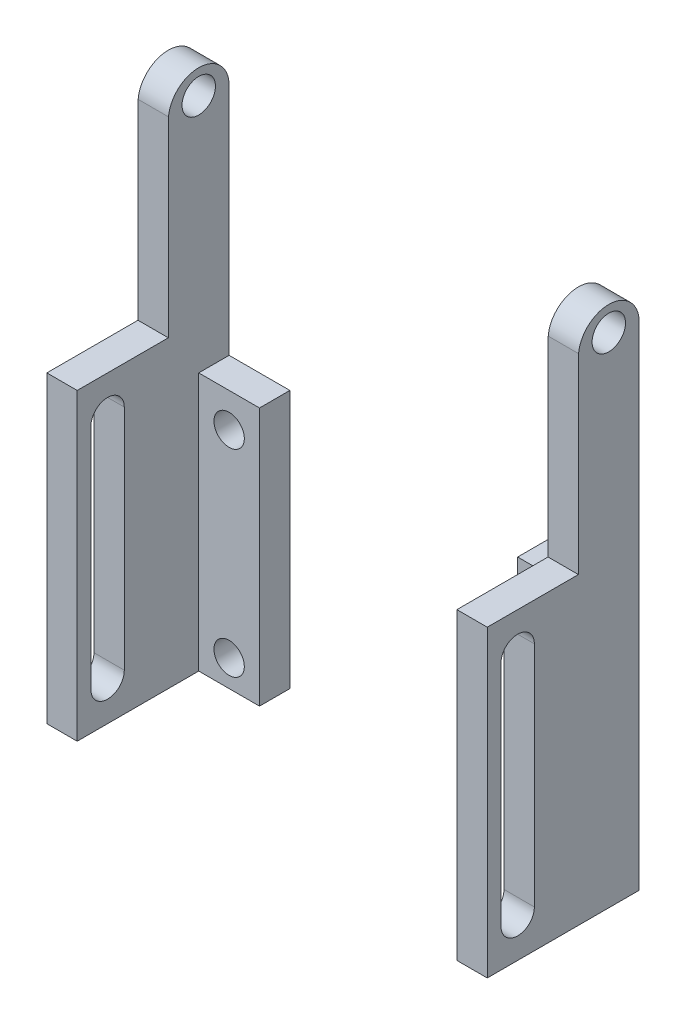
SolidWorks part; units mm, degrees
ref_plane "前视基准面" through (0, 0, 0) normal (0, 0, 1) x (1, 0, 0)
ref_plane "上视基准面" through (0, 0, 0) normal (0, 1, 0) x (1, 0, 0)
ref_plane "右视基准面" through (0, 0, 0) normal (1, 0, 0) x (0, 0, -1)
sketch "草图1" plane through (0, 0, 0) normal (0, 0, 1) x (1, 0, 0)
  line L16 (-39.25, -3) -> (-41.25, -3)
  line L17 (-41.25, -3) -> (-41.25, -7)
  line L18 (-41.25, -7) -> (-39.25, -7)
  line L19 (-39.25, -7) -> (-39.25, -3)
  line L20 (-34.75, -3) -> (-36.75, -3)
  line L21 (-36.75, -3) -> (-36.75, -7)
  line L22 (-36.75, -7) -> (-34.75, -7)
  line L23 (-34.75, -7) -> (-34.75, -3)
  line L24 (-12.25, -3) -> (-14.25, -3)
  line L25 (-14.25, -3) -> (-14.25, -7)
  line L26 (-14.25, -7) -> (-12.25, -7)
  line L27 (-12.25, -7) -> (-12.25, -3)
  line L28 (-7.75, -3) -> (-9.75, -3)
  line L29 (-9.75, -3) -> (-9.75, -7)
  line L30 (-9.75, -7) -> (-7.75, -7)
  line L31 (-7.75, -7) -> (-7.75, -3)
  line L32 (-9.75, -5) -> (-12.25, -5) construction
  line L33 (-36.75, -5) -> (-39.25, -5) construction
  line L34 (-9.75, -3) -> (-39.25, -3) construction
  line L35 (-24.5, -3) -> (-24.5, -18.3575) construction
  line L36 (-38.9967, -3) -> (-36.9967, -3)
  line L37 (-10.0033, -3) -> (-12.0033, -3)
  line L38 (-10.0033, -3) -> (-10.0033, -38)
  line L39 (-10.0033, -38) -> (-12.0033, -38)
  line L40 (-12.0033, -3) -> (-12.0033, -38)
  line L41 (-36.9967, -3) -> (-36.9967, -38)
  line L42 (-38.9967, -3) -> (-38.9967, -38)
  line L43 (-38.9967, -38) -> (-36.9967, -38)
  dimension "D1" = 2
  dimension "D2" = 0.2533
  dimension "D3" = 35
extrude "凸台-拉伸1" add sketch "草图1" against normal blind 4 contours L38 L39 L40 L37 | L41 L43 L42 L36
sketch "草图2" plane through (0, 0, -4) normal (0, 0, -1) x (-1, 0, 0)
  line L1 (36.9967, -38) -> (32.9967, -38)
  line L2 (36.9967, -38) -> (36.9967, -21)
  line L3 (36.9967, -21) -> (32.9967, -21)
  line L4 (38.9967, -3) -> (36.9967, -3)
  line L5 (36.9967, -3) -> (36.9967, -38)
  line L6 (36.9967, -38) -> (38.9967, -38)
  line L7 (38.9967, -38) -> (38.9967, -3)
  line L8 (38.9967, -3) -> (36.9967, -3)
  line L9 (36.9967, -3) -> (36.9967, -38)
  line L10 (36.9967, -38) -> (38.9967, -38)
  line L11 (38.9967, -38) -> (38.9967, -3)
  line L12 (12.0033, -3) -> (10.0033, -3)
  line L13 (10.0033, -3) -> (10.0033, -38)
  line L14 (10.0033, -38) -> (12.0033, -38)
  line L15 (12.0033, -38) -> (12.0033, -3)
  line L16 (12.0033, -3) -> (10.0033, -3)
  line L17 (10.0033, -3) -> (10.0033, -38)
  line L18 (10.0033, -38) -> (12.0033, -38)
  line L19 (12.0033, -38) -> (12.0033, -3)
  line L20 (32.9967, -38) -> (32.9967, -21)
  line L21 (12.0033, -38) -> (16.0033, -38)
  line L22 (12.0033, -38) -> (12.0033, -21)
  line L23 (12.0033, -21) -> (16.0033, -21)
  line L24 (16.0033, -38) -> (16.0033, -21)
  line M14 (36.9967, -3) -> (36.9967, -38)
  dimension "D3" = 4
  dimension "D4" = 17
  dimension "D5" = 4
  dimension "D6" = 17
  dimension "D1" = 0
  dimension "D2" = 0
extrude "凸台-拉伸2" add sketch "草图2" against normal blind 2 contours L20 L1 L3 M14 | L21 L24 L23 L19
sketch "草图3" plane through (0, 0, -4) normal (0, 0, -1) x (-1, 0, 0)
  line L0 (32.9967, -38) -> (16.0033, -38) construction
  line L1 (24.5, -38) -> (24.5, -20.7583) construction
  line L6 (12.0033, -3) -> (10.0033, -3)
  line L7 (10.0033, -3) -> (10.0033, -38)
  line L8 (10.0033, -38) -> (16.0033, -38)
  line L9 (16.0033, -38) -> (16.0033, -21)
  line L10 (16.0033, -21) -> (12.0033, -21)
  line L11 (12.0033, -21) -> (12.0033, -3)
  line L12 (12.0033, -3) -> (10.0033, -3)
  line L13 (10.0033, -3) -> (10.0033, -38)
  line L14 (10.0033, -38) -> (16.0033, -38)
  line L15 (16.0033, -38) -> (16.0033, -21)
  line L16 (16.0033, -21) -> (12.0033, -21)
  line L17 (12.0033, -21) -> (12.0033, -3)
  line L18 (38.9967, -3) -> (36.9967, -3)
  line L19 (36.9967, -3) -> (36.9967, -21)
  line L20 (36.9967, -21) -> (32.9967, -21)
  line L21 (32.9967, -21) -> (32.9967, -38)
  line L22 (32.9967, -38) -> (38.9967, -38)
  line L23 (38.9967, -38) -> (38.9967, -3)
  line L24 (38.9967, -3) -> (36.9967, -3)
  line L25 (36.9967, -3) -> (36.9967, -21)
  line L26 (36.9967, -21) -> (32.9967, -21)
  line L27 (32.9967, -21) -> (32.9967, -38)
  line L28 (32.9967, -38) -> (38.9967, -38)
  line L29 (38.9967, -38) -> (38.9967, -3)
  circle A0 centre (34.9967, -36.2462) radius 1
  circle A1 centre (34.9967, -23.2462) radius 1
  circle A2 centre (14.0033, -23.2462) radius 1
  circle A3 centre (14.0033, -36.2462) radius 1
  dimension "D4" = 2
  dimension "D5" = 2
  dimension "D6" = 2
  dimension "D7" = 2
  dimension "D8" = 13
  dimension "D3" = 17
  dimension "D1" = 0
  dimension "D2" = 0
extrude "切除-拉伸1" cut sketch "草图3" against normal blind 2 contours A0 | A1 | A3 | A2
sketch "草图5" plane through (0, 0, 0) normal (0, 0, 1) x (1, 0, 0)
  line L1 (-10.0033, -38) -> (-12.0033, -38)
  line L2 (-10.0033, -38) -> (-10.0033, -18)
  line L3 (-10.0033, -18) -> (-12.0033, -18)
  line L4 (-10.0033, -3) -> (-12.0033, -3)
  line L5 (-12.0033, -3) -> (-12.0033, -38)
  line L6 (-12.0033, -38) -> (-10.0033, -38)
  line L7 (-10.0033, -38) -> (-10.0033, -3)
  line L8 (-10.0033, -3) -> (-12.0033, -3)
  line L9 (-12.0033, -3) -> (-12.0033, -38)
  line L10 (-12.0033, -38) -> (-10.0033, -38)
  line L11 (-10.0033, -38) -> (-10.0033, -3)
  line L12 (-36.9967, -3) -> (-38.9967, -3)
  line L13 (-38.9967, -3) -> (-38.9967, -38)
  line L14 (-38.9967, -38) -> (-36.9967, -38)
  line L15 (-36.9967, -38) -> (-36.9967, -3)
  line L16 (-36.9967, -3) -> (-38.9967, -3)
  line L17 (-38.9967, -3) -> (-38.9967, -38)
  line L18 (-38.9967, -38) -> (-36.9967, -38)
  line L19 (-36.9967, -38) -> (-36.9967, -3)
  line L20 (-12.0033, -38) -> (-12.0033, -18)
  line L21 (-36.9967, -38) -> (-38.9967, -38)
  line L22 (-36.9967, -38) -> (-36.9967, -18)
  line L23 (-36.9967, -18) -> (-38.9967, -18)
  line L24 (-38.9967, -38) -> (-38.9967, -18)
  line M12 (-12.0033, -3) -> (-12.0033, -38)
  line M13 (-12.0033, -38) -> (-10.0033, -38)
  line M14 (-10.0033, -38) -> (-10.0033, -3)
  dimension "D3" = 20
  dimension "D4" = 20
  dimension "D1" = 0
  dimension "D2" = 0
extrude "凸台-拉伸3" add sketch "草图5" along normal blind 6 contours L3 M14 M12 M13 | L19 L23 L17 L18
sketch "草图6" plane through (-10.0033, 0, 0) normal (1, 0, 0) x (0, 0, -1)
  line L0 (-4, -18) -> (-4, -38) construction
  line L1 (-4, -20.5) -> (-4, -35.5) construction
  line L2 (-2.9, -20.5) -> (-2.9, -35.5)
  line L3 (-5.1, -20.5) -> (-5.1, -35.5)
  line L4 (-6, -18) -> (-6, -38) construction
  line L6 (0, -3) -> (0, -18)
  line L7 (0, -18) -> (-6, -18)
  line L8 (-6, -18) -> (-6, -38)
  line L9 (-6, -38) -> (4, -38)
  line L10 (4, -38) -> (4, -3)
  line L11 (4, -3) -> (0, -3)
  line L12 (0, -3) -> (0, -18)
  line L13 (0, -18) -> (-6, -18)
  line L14 (-6, -18) -> (-6, -38)
  line L15 (-6, -38) -> (4, -38)
  line L16 (4, -38) -> (4, -3)
  line L17 (4, -3) -> (0, -3)
  arc A0 (-2.9, -20.5) -> (-5.1, -20.5) centre (-4, -20.5) ccw
  arc A1 (-5.1, -35.5) -> (-2.9, -35.5) centre (-4, -35.5) ccw
  point P10 (-4, -28)
  dimension "D2" = 2.2
  dimension "D3" = 15
  dimension "D4" = 2
  dimension "D1" = 0
extrude "切除-拉伸2" cut sketch "草图6" against normal through all contours L3 A1 L2 A0
sketch "草图7" plane through (-10.0033, 0, 0) normal (1, 0, 0) x (0, 0, -1)
  line L0 (2, -6.3) -> (2, -4.1) construction
  line L6 (0, -3) -> (0, -18)
  line L7 (0, -18) -> (-6, -18)
  line L8 (-6, -18) -> (-6, -38)
  line L9 (-6, -38) -> (4, -38)
  line L10 (4, -38) -> (4, -3)
  line L11 (4, -3) -> (0, -3)
  line L12 (0, -3) -> (0, -18)
  line L13 (0, -18) -> (-6, -18)
  line L14 (-6, -18) -> (-6, -38)
  line L15 (-6, -38) -> (4, -38)
  line L16 (4, -38) -> (4, -3)
  line L17 (4, -3) -> (0, -3)
  line L18 (0.9, -5.2) -> (3.1, -5.2) construction
  circle A0 centre (2, -5.2) radius 1.1 construction
  arc A1 (4, -5.4) -> (0, -5.4) centre (2, -5.4) ccw
  point P14 (2, -5.2)
  dimension "D2" = 0.2
  dimension "D1" = 0
extrude "切除-拉伸3" cut sketch "草图7" against normal through all contours A1 L16 L9
sketch "草图8" plane through (-10.0033, 0, 0) normal (1, 0, 0) x (0, 0, -1)
  line L5 (0, -5.4) -> (0, -18)
  line L6 (0, -18) -> (-6, -18)
  line L7 (-6, -18) -> (-6, -38)
  line L8 (-6, -38) -> (4, -38)
  line L9 (4, -38) -> (4, -5.4)
  line L10 (0, -5.4) -> (0, -18)
  line L11 (0, -18) -> (-6, -18)
  line L12 (-6, -18) -> (-6, -38)
  line L13 (-6, -38) -> (4, -38)
  line L14 (4, -38) -> (4, -5.4)
  arc A1 (4, -5.4) -> (0, -5.4) centre (2, -5.4) ccw
  arc A2 (4, -5.4) -> (0, -5.4) centre (2, -5.4) ccw
  circle A3 centre (2, -5.6) radius 2
  circle A4 centre (2, -5.4) radius 2
  dimension "D2" = 0.2
  dimension "D1" = 0
extrude "切除-拉伸4" cut sketch "草图8" against normal through all
sketch "草图9" plane through (-10.0033, 0, 0) normal (1, 0, 0) x (0, 0, -1)
  line L5 (0, -5.4) -> (0, -18)
  line L6 (0, -18) -> (-6, -18)
  line L7 (-6, -18) -> (-6, -38)
  line L8 (-6, -38) -> (4, -38)
  line L9 (4, -38) -> (4, -5.4)
  line L10 (0, -5.4) -> (0, -18)
  line L11 (0, -18) -> (-6, -18)
  line L12 (-6, -18) -> (-6, -38)
  line L13 (-6, -38) -> (4, -38)
  line L14 (4, -38) -> (4, -5.4)
  circle A0 centre (2, -5.2) radius 1.1
  arc A2 (3.9975, -5.5) -> (0.0025, -5.5) centre (2, -5.6) ccw
  arc A9 (3.9975, -5.5) -> (0.0025, -5.5) centre (2, -5.6) ccw
  arc A10 (0, -5.4) -> (0.0025, -5.5) centre (2, -5.4) ccw
  arc A11 (0, -5.4) -> (0.0025, -5.5) centre (2, -5.4) ccw
  arc A12 (3.9975, -5.5) -> (4, -5.4) centre (2, -5.4) ccw
  arc A13 (3.9975, -5.5) -> (4, -5.4) centre (2, -5.4) ccw
  dimension "D2" = 2.2
  dimension "D1" = 0
extrude "切除-拉伸5" cut sketch "草图9" against normal through all contours A0
